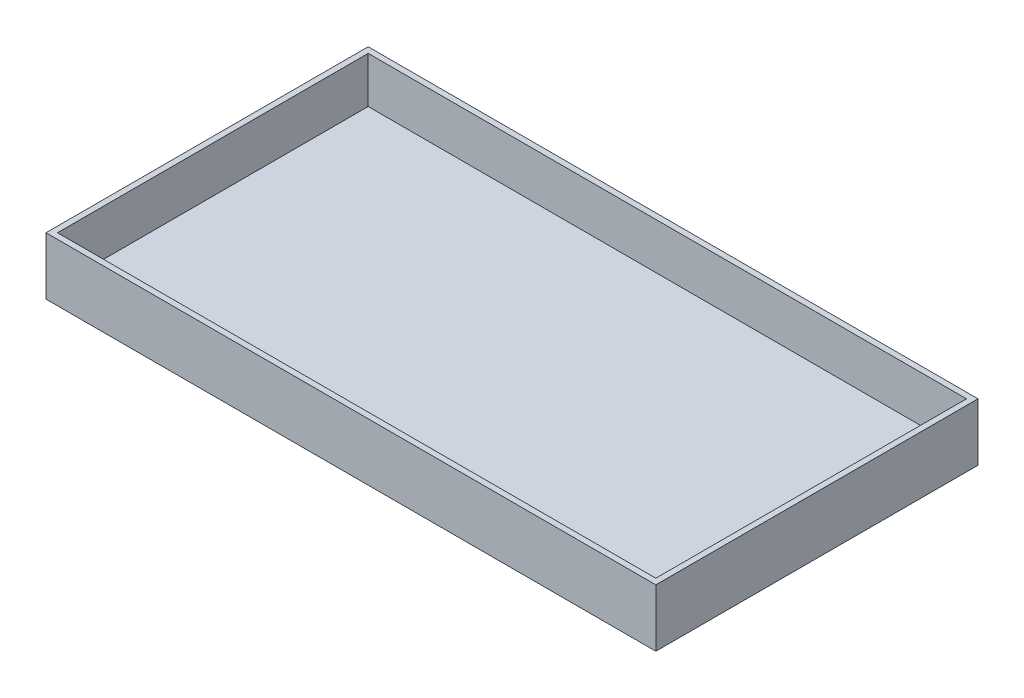
SolidWorks part; units mm, degrees
ref_plane "Front Plane" through (0, 0, 0) normal (0, 0, 1) x (1, 0, 0)
ref_plane "Top Plane" through (0, 0, 0) normal (0, 1, 0) x (1, 0, 0)
ref_plane "Right Plane" through (0, 0, 0) normal (1, 0, 0) x (0, 0, -1)
sketch "Sketch1" plane through (0, 0, 0) normal (0, 1, 0) x (1, 0, 0)
  line L1 (-53, 28) -> (53, 28)
  line L2 (-53, 28) -> (-53, -28)
  line L3 (-53, -28) -> (53, -28)
  line L4 (53, 28) -> (53, -28)
  line L5 (-53, 28) -> (53, -28) construction
  line L6 (-53, -28) -> (53, 28) construction
  line L7 (-52, 27) -> (52, 27)
  line L8 (-52, 27) -> (-52, -27)
  line L9 (-52, -27) -> (52, -27)
  line L10 (52, 27) -> (52, -27)
  line L11 (-52, 27) -> (52, -27) construction
  line L12 (-52, -27) -> (52, 27) construction
  point P0 (0, 0)
  point P6 (0, 0)
  dimension "D1" = 56
  dimension "D2" = 106
  dimension "D3" = 54
  dimension "D4" = 104
extrude "Boss-Extrude1" add sketch "Sketch1" along normal blind 10
sketch "Sketch2" plane through (0, 0, 0) normal (0, 1, 0) x (1, 0, 0)
  line L1 (-53, -28) -> (53, -28)
  line L2 (-53, -28) -> (-53, 28)
  line L3 (-53, 28) -> (53, 28)
  line L4 (53, -28) -> (53, 28)
  line L5 (-53, -28) -> (53, 28) construction
  line L6 (-53, 28) -> (53, -28) construction
  point P0 (0, 0)
  dimension "D1" = 106
  dimension "D2" = 56
extrude "Boss-Extrude2" add sketch "Sketch2" along normal blind 2
